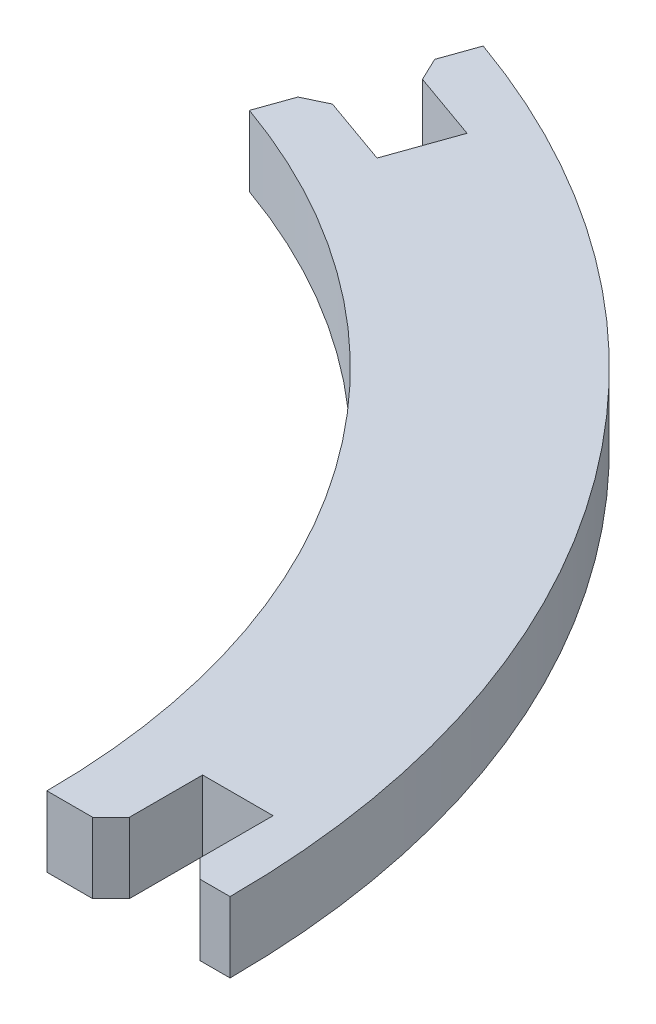
SolidWorks part; units mm, degrees
ref_plane "Front" through (0, 0, 0) normal (0, 0, 1) x (1, 0, 0)
ref_plane "Top" through (0, 0, 0) normal (0, 1, 0) x (1, 0, 0)
ref_plane "Right" through (0, 0, 0) normal (1, 0, 0) x (0, 0, -1)
sketch "Sketch1" plane through (0, 0, 0) normal (0, 1, 0) x (1, 0, 0)
  line L0 (-51.8779, -0.1658) -> (-35.6803, 45.5746) construction
  line L1 (-51.8779, -0.1658) -> (-13.6887, -0.1658) construction
  line L2 (-35.1875, 46.9663) -> (-36.214, 44.0677)
  line L3 (-11.8779, -0.1658) -> (-8.377, -0.1658)
  line L4 (-40.0422, 43.3812) -> (-34.1302, 41.2876) construction
  line L5 (-36.214, 44.0677) -> (-31.5008, 42.3986)
  line L6 (-6.452, -0.1673) -> (-6.452, 6.6231) construction
  line L7 (-37.4991, 40.4385) -> (-32.7859, 38.7695)
  line L8 (-31.5008, 42.3986) -> (-32.7859, 38.7695)
  line L9 (-37.4991, 40.4385) -> (-38.5256, 37.5399)
  line L10 (-4.527, -0.1658) -> (-1.8779, -0.1658)
  line L11 (-8.377, -0.1658) -> (-8.377, 4.8342)
  line L12 (-8.377, 4.8342) -> (-4.527, 4.8342)
  line L13 (-4.527, -0.1658) -> (-4.527, 4.8342)
  circle A0 centre (-51.8779, -0.1658) radius 50 construction
  circle A1 centre (-51.877, -0.1673) radius 40 construction
  arc A2 (-38.5256, 37.5399) -> (-11.8779, -0.1658) centre (-51.8779, -0.1658) cw
  arc A3 (-35.1875, 46.9663) -> (-1.8779, -0.1658) centre (-51.8779, -0.1658) cw
  dimension "D1" = 50
  dimension "D7" = 40
  dimension "D2" = 3.85
  dimension "D3" = 5
  dimension "D5" = 3.85
  dimension "D6" = 70.5
  dimension "D8" = 5
extrude "Boss-Extrude1" add sketch "Sketch1" along normal blind 3.85 contours A3 L10 L13 L12 L11 L3 A2 L9 L7 L8 L5 L2
chamfer "Chamfer1" distance 1 angle 45 4 edges at (-37.4991, 1.925, -40.4385) (-36.214, 1.925, -44.0677) (-8.377, 1.925, 0.1658) (-4.527, 1.925, 0.1658)
equation "\"entrance\"=5"
equation "\"D3@Sketch1\"=\"entrance\""
equation "\"D2@Sketch1\" = \"thick\""
equation "\"D5@Sketch1\" = \"thick\""
equation "\"D8@Sketch1\"=\"entrance\""
equation "\"D1@Boss-Extrude1\"= \"thick\""
equation "\"thick\"=3.85"
